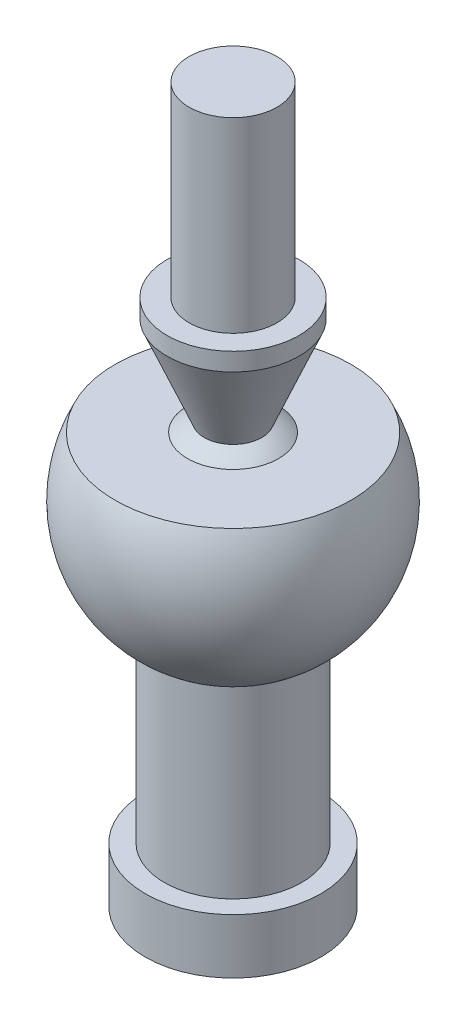
SolidWorks part; units mm, degrees
ref_plane "前视基准面" through (0, 0, 0) normal (0, 0, 1) x (1, 0, 0)
ref_plane "上视基准面" through (0, 0, 0) normal (0, 1, 0) x (1, 0, 0)
ref_plane "右视基准面" through (0, 0, 0) normal (1, 0, 0) x (0, 0, -1)
sketch "草图1" plane through (0, 0, 0) normal (0, 0, 1) x (1, 0, 0)
  line L0 (0, 0.1122) -> (0, 28.5643) construction
  line L1 (0, 12.0381) -> (4, 9.7287)
  line L2 (4, 9.7287) -> (4, 0)
  line L3 (4, 0) -> (8, 0)
  line L4 (8, 0) -> (8, 5)
  line L5 (8, 5) -> (6.25, 5)
  line L6 (6.25, 5) -> (6.25, 21.7561)
  line L7 (4.1491, 37.3738) -> (10.7295, 37.3738)
  line L8 (0, 38.2646) -> (2.6169, 38.2646) construction
  line L9 (2.6169, 38.2646) -> (6, 46.3632)
  line L10 (6, 46.3632) -> (6, 48)
  line L11 (6, 48) -> (4, 48)
  line L12 (4, 48) -> (4, 65)
  line L13 (4, 65) -> (0, 65)
  line L14 (2.6169, 38.2646) -> (0, 32) construction
  line L15 (0, 32) -> (4.1491, 37.3738) construction
  line L16 (0, 12.0381) -> (0, 65)
  arc A0 (6.25, 21.7561) -> (10.7295, 37.3738) centre (0, 32) ccw
  arc A1 (4.1491, 37.3738) -> (2.6169, 38.2646) centre (0, 32) ccw
  dimension "D11" = 12
  dimension "D1" = 65
  dimension "D2" = 8
  dimension "D3" = 8
  dimension "D4" = 32
  dimension "D5" = 16
  dimension "D6" = 12
  dimension "D7" = 5
  dimension "D8" = 12.5
  dimension "D9" = 16
  dimension "D10" = 60
  dimension "D12" = 15
revolve "旋转1" add sketch "草图1" angle 360 about L0
